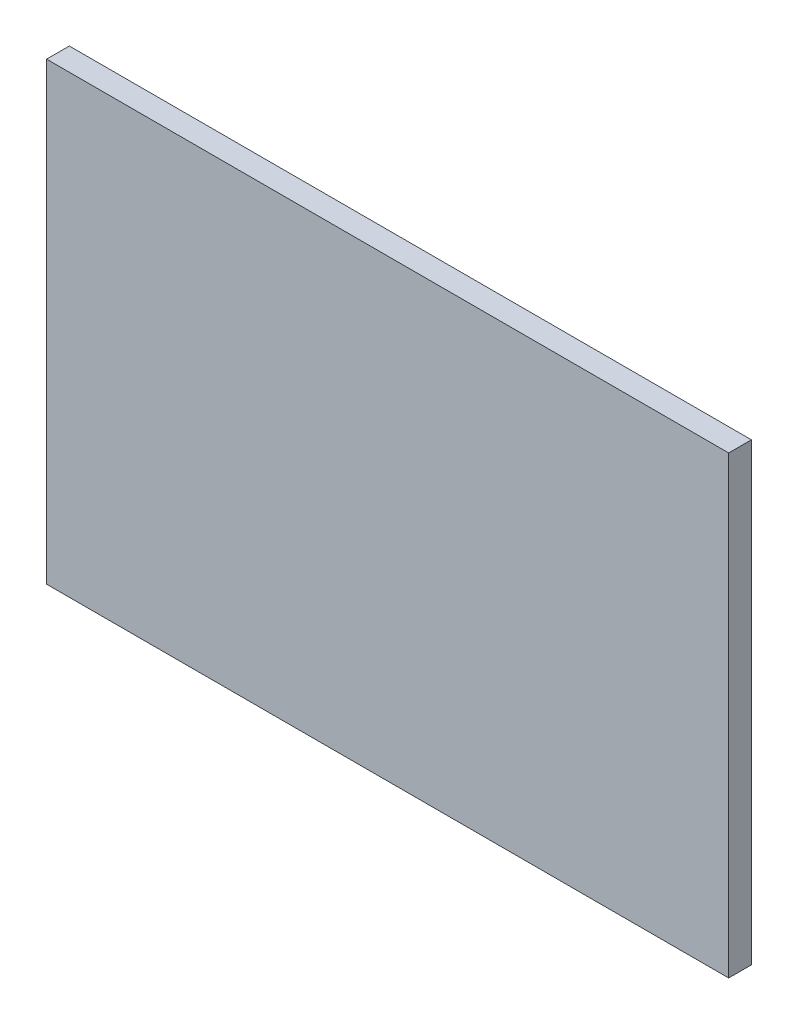
SolidWorks part; units mm, degrees
ref_plane "Alzado" through (0, 0, 0) normal (0, 0, 1) x (1, 0, 0)
ref_plane "Planta" through (0, 0, 0) normal (0, 1, 0) x (1, 0, 0)
ref_plane "Vista lateral" through (0, 0, 0) normal (1, 0, 0) x (0, 0, -1)
sketch "Croquis1" plane through (0, 0, 0) normal (0, 0, 1) x (1, 0, 0)
  line L1 (-72.2025, 35.0322) -> (-42.2025, 35.0322)
  line L2 (-72.2025, 35.0322) -> (-72.2025, 15.0322)
  line L3 (-72.2025, 15.0322) -> (-42.2025, 15.0322)
  line L4 (-42.2025, 35.0322) -> (-42.2025, 15.0322)
  dimension "D1" = 30
  dimension "D2" = 20
extrude "Saliente-Extruir1" add sketch "Croquis1" along normal blind 1
